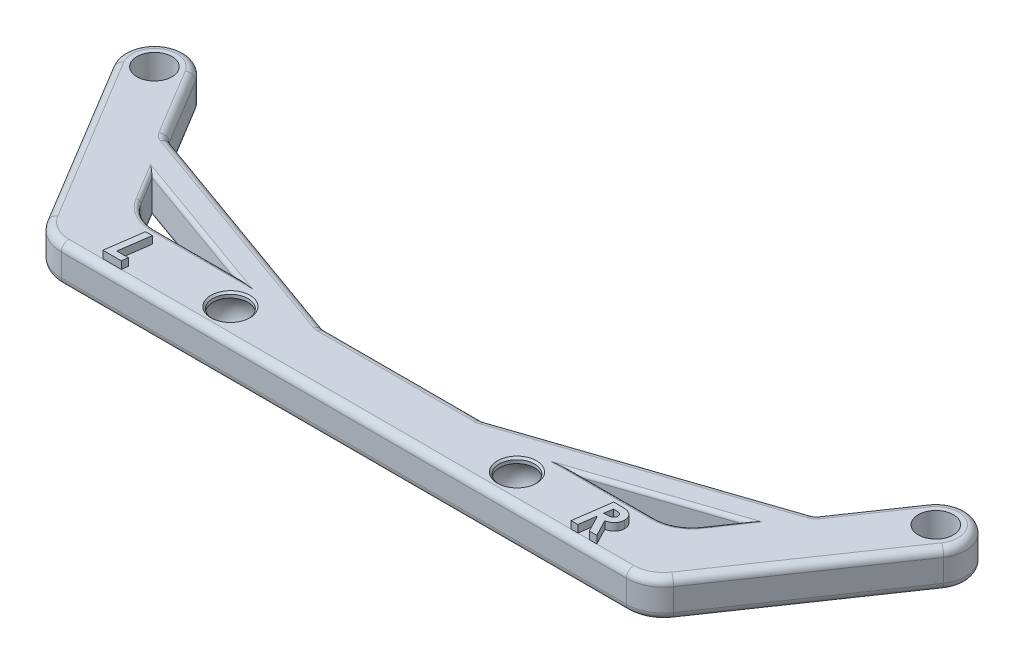
SolidWorks part; units mm, degrees
ref_plane "Front Plane" through (0, 0, 0) normal (0, 0, 1) x (1, 0, 0)
ref_plane "Top Plane" through (0, 0, 0) normal (0, 1, 0) x (1, 0, 0)
ref_plane "Right Plane" through (0, 0, 0) normal (1, 0, 0) x (0, 0, -1)
sketch "Sketch1" plane through (0, 0, 0) normal (0, 1, 0) x (1, 0, 0)
  line L0 (-38.3668, 0) -> (38.3668, 0)
  line L1 (0, 36) -> (0, 0) construction
  line L2 (-38.3668, 0) -> (-52.0834, 22.7282)
  line L3 (38.3668, 0) -> (53.3446, 21.9175)
  line L4 (-19.1834, 0) -> (-19.1834, -21) construction
  line L5 (19.1834, 0) -> (19.1834, -21) construction
  line L6 (37.7446, 6.1789) -> (50.0421, 24.1744)
  line L7 (-33.2864, 4) -> (33.6164, 4)
  line L8 (-37.5672, 6.4165) -> (-48.6587, 24.795)
  line L9 (41.9672, -1.8211) -> (56.6471, 19.6607)
  line L10 (-37.8023, -4) -> (37.839, -4)
  line L11 (-42.0832, -1.5835) -> (-55.5081, 20.6614)
  line L12 (40.4781, -4) -> (56.6471, 19.6607) construction
  line L13 (-40.6248, -4) -> (40.4781, -4) construction
  line L14 (36.2555, 4) -> (50.0421, 24.1744) construction
  line L15 (-36.1089, 4) -> (36.2555, 4) construction
  line L16 (-36.1089, 4) -> (-48.6587, 24.795) construction
  line L17 (-40.6248, -4) -> (-55.5081, 20.6614) construction
  line L18 (-43.113, 15.6057) -> (-10.6834, 4)
  line L19 (43.8933, 15.1767) -> (10.6834, 4)
  line L20 (23.2239, 4) -> (40.1478, 9.6957)
  line L21 (-39.8427, 10.1869) -> (-22.5547, 4)
  circle A0 centre (-52.0834, 22.7282) radius 2.35
  circle A1 centre (53.3446, 21.9175) radius 2.35
  circle A2 centre (-19.1834, 0) radius 2
  circle A3 centre (19.1834, 0) radius 2
  arc A4 (-55.5081, 20.6614) -> (-48.6587, 24.795) centre (-52.0834, 22.7282) cw
  arc A5 (50.0421, 24.1744) -> (56.6471, 19.6607) centre (53.3446, 21.9175) cw
  arc A6 (41.9672, -1.8211) -> (37.839, -4) centre (37.839, 1) cw
  arc A7 (37.7446, 6.1789) -> (33.6164, 4) centre (33.6164, 9) cw
  arc A8 (-33.2864, 4) -> (-37.5672, 6.4165) centre (-33.2864, 9) cw
  arc A9 (-37.8023, -4) -> (-42.0832, -1.5835) centre (-37.8023, 1) cw
  point P5 (-19.1834, 0)
  point P6 (19.1834, 0)
  point P41 (45.8557, 10.9588)
  point P42 (43.8933, 15.1767)
  dimension "D9" = 4.7
  dimension "D10" = 4.7
  dimension "D11" = 4
  dimension "D12" = 4
  dimension "D14" = 5
  dimension "D1" = 76.7337
  dimension "D2" = 36
  dimension "D3" = 19.1834
  dimension "D4" = 26.5464
  dimension "D5" = 121.111
  dimension "D6" = 26.5464
  dimension "D7" = 124.348
  dimension "D8" = 21
  dimension "D15" = 4
  dimension "D16" = 4
  dimension "D17" = 8.5
  dimension "D18" = 8.5
  dimension "D13" = 4
extrude "Boss-Extrude1" add sketch "Sketch1" along normal blind 5
fillet "Fillet2" radius 0.5 16 edges at (-27.9205, 5, -4) (-27.9205, 0, -4) (-38.705, 5, -8.3017) (-38.705, 0, -8.3017) (38.9462, 0, -7.9373) (38.9462, 5, -7.9373) (35.9504, 0, -4.5782) (35.9504, 5, -4.5782) (-35.7443, 0, -4.6458) (-35.7443, 5, -4.6458) (31.6858, 0, -6.8478) (31.6858, 5, -6.8478) (28.4202, 5, -4) (28.4202, 0, -4) (-31.1987, 0, -7.0935) (-31.1987, 5, -7.0935)
fillet "Fillet3" radius 1 28 edges at (0, 5, -4) (0, 0, -4) (27.2884, 0, -9.5883) (27.2884, 5, -9.5883) (-26.8982, 0, -9.8029) (-26.8982, 5, -9.8029) (46.9677, 5, -19.6755) (46.9677, 0, -19.6755) (55.6015, 0, -25.2201) (55.6015, 5, -25.2201) (49.3072, 0, -8.9198) (49.3072, 5, -8.9198) (40.173, 0, 3.4218) (40.173, 5, 3.4218) (0.0183, 0, 4) (0.0183, 5, 4) (-40.2602, 0, 3.3542) (-40.2602, 5, 3.3542) (-45.8858, 0, -20.2003) (-45.8858, 5, -20.2003) (-54.1502, 0, -26.1528) (-54.1502, 5, -26.1528) (-48.7956, 0, -9.5389) (-48.7956, 5, -9.5389) (43.8933, 2.5, -15.1767) (-43.113, 2.5, -15.6057) (10.6834, 2.5, -4) (-10.6834, 2.5, -4)
sketch3d "3DSketch1" plane through (0, 0, 0) normal (0, 0, 1) x (1, 0, 0)
  dimension "D1" = 2.5
sketch3d "3DSketch2"
  line L0 (-19.1834, 5, 0) -> (-19.1834, 0, 0)
  line L1 (19.1834, 5, 0) -> (19.1834, 0, 0)
  circle A0 centre (-19.1834, 0, 0) radius 2 construction
  circle A1 centre (-19.1834, 5, 0) radius 2 construction
  circle A2 centre (-19.1834, 0, 0) radius 2
  circle A3 centre (-19.1834, 5, 0) radius 2
  circle A4 centre (19.1834, 5, 0) radius 2
  circle A5 centre (19.1834, 0, 0) radius 2
  point P2 (-19.1834, 2, 0)
  point P5 (-19.1834, 7, 0)
  point P7 (-19.1834, 2, 0)
  point P9 (-19.1834, 7, 0)
  point P10 (-19.1834, 2.5, 0)
  point P13 (19.1834, 7, 0)
  point P16 (19.1834, 2, 0)
  point P17 (19.1834, 2.5, 0)
sketch3d "3DSketch3"
  line L0 (-19.1834, 5, 0) -> (-19.1834, 0, 0) construction
  line L1 (19.1834, 5, 0) -> (19.1834, 0, 0) construction
sketch "Sketch2" plane through (0, 0, 0) normal (0, 0, 1) x (1, 0, 0)
  line L0 (19.1834, 5) -> (19.1834, 0) construction
  line L2 (19.1834, 5) -> (19.1834, 0)
  line L3 (-19.1834, 5.475) -> (-19.1834, -0.475)
  line L4 (0, 0) -> (0.0183, 5) construction
  line L5 (-37.8023, 5) -> (37.839, 5) construction
  line L7 (-19.1834, 7.5232) -> (-19.1834, -1.7698) construction
  line L8 (-21.5461, 5) -> (-21.5461, 4.3079)
  line L9 (-22.1584, 2.5) -> (-19.1834, 2.5) construction
  line L10 (-21.5461, 0) -> (-21.5461, 0.6921)
  line L11 (-21.5461, 5) -> (-19.1834, 5)
  line L12 (-19.1834, 5) -> (-19.1834, 0)
  line L13 (-19.1834, 0) -> (-21.5461, 0)
  arc A0 (-21.5461, 4.3079) -> (-21.5461, 0.6921) centre (-19.1834, 2.5) ccw
  circle A1 centre (19.2012, 2.3593) radius 2.975
  point P0 (-19.1834, 2.5)
  point P2 (19.1834, 2.5)
  point P24 (-22.1584, 2.5)
  dimension "D1" = 5.95
  dimension "D2" = 2.3626
revolve "Cut-Revolve3" cut sketch "Sketch2" angle 360 about L7
mirror "Mirror1" about plane through (0, 0, 0) normal (1, 0, 0) of "Cut-Revolve3"
chamfer "Chamfer1" distance 0.25 angle 45 4 edges at (19.1834, 0, 2.3626) (19.1834, 5, 2.3626) (-19.1834, 0, 2.3626) (-19.1834, 5, 2.3626)
sketch "Sketch3" plane through (0, 5, 0) normal (0, 1, 0) x (1, 0, 0)
  line L0 (-37.8023, -3) -> (37.839, -3) construction
  line L1 (0.0049, 3) -> (0.0183, -3) construction
  line L2 (10.5197, 3) -> (-10.5099, 3) construction
  text T0 "<b><i>L                               R</i></b>" font "Century Gothic" height 5
  point P9 (-0.9109, 1.253)
  point P10 (0.0116, 0)
extrude "Boss-Extrude2" add sketch "Sketch3" along normal blind 1
